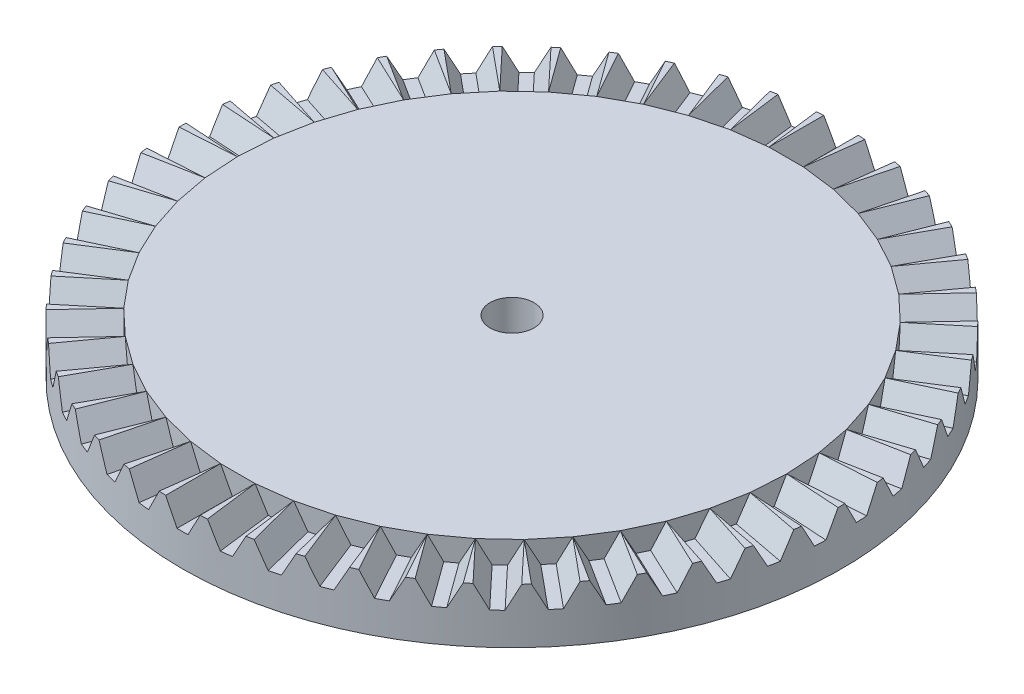
SolidWorks part; units mm, degrees
ref_plane "Front Plane" through (0, 0, 0) normal (0, 0, 1) x (1, 0, 0)
ref_plane "Top Plane" through (0, 0, 0) normal (0, 1, 0) x (1, 0, 0)
ref_plane "Right Plane" through (0, 0, 0) normal (1, 0, 0) x (0, 0, -1)
sketch "Foot Measurements" [suppressed] plane through (0, 0, 0) normal (0, 1, 0) x (1, 0, 0)
  line L0 (0, 0) -> (0, 73) construction
  line L1 (0, 0) -> (0, 147) construction
  line L2 (0, 0) -> (33, 0) construction
  line L3 (0, 0) -> (75, 0) construction
  line L4 (0, 73) -> (33, 73) construction
  line L5 (33, 73) -> (33, 0) construction
  line L6 (0, 147) -> (75, 147) construction
  line L7 (75, 147) -> (75, 0) construction
  line L8 (0, -100) -> (250, -100) construction
  line L9 (0, -100) -> (173, -100) construction
  dimension "D1" = 33
  dimension "D2" = 75
  dimension "D3" = 73
  dimension "D4" = 147
sketch "Sketch3" plane through (0, 0, 0) normal (0, 1, 0) x (1, 0, 0)
  circle A0 centre (0, 0) radius 30
extrude "Boss-Extrude3" add sketch "Sketch3" along normal blind 5
sketch "Sketch6" plane through (0, 5, 0) normal (0, 1, 0) x (1, 0, 0)
  circle A1 centre (0, 0) radius 2
  dimension "D1" = 4
extrude "Cut-Extrude1" cut sketch "Sketch6" against normal up to next
sketch "Sketch5" plane through (0, 5, 0) normal (0, 1, 0) x (1, 0, 0)
  line L0 (-1.5701, 29.9589) -> (-1.5701, 24.9589)
  line L1 (-1.5701, 24.9589) -> (1.5701, 24.9589)
  line L2 (1.5701, 24.9589) -> (1.5701, 29.9589)
  line L4 (0, 0) -> (-1.5701, 29.9589) construction
  line L5 (0, 0) -> (1.5701, 29.9589) construction
  circle A1 centre (0, 0) radius 30 construction
  arc A2 (1.5701, 29.9589) -> (-1.5701, 29.9589) centre (0, 0) ccw
  dimension "D1" = 3.1402
  dimension "D2" = 6
  dimension "D3" = 5
extrude "Cut-Extrude2" cut sketch "Sketch5" against normal blind 3
sketch "Sketch7" plane through (0, 0, -24.9589) normal (0, 0, -1) x (-1, 0, 0)
  line L0 (-1.5701, 2) -> (1.5701, 2)
  line L1 (1.5701, 2) -> (1.5701, 5)
  line L2 (1.5701, 5) -> (0.4972, 2.95)
  line L3 (-0.4972, 2.95) -> (-1.5701, 5)
  line L4 (-1.5701, 2) -> (-1.5701, 5)
  line L5 (-0.4972, 2.95) -> (0.4972, 2.95)
  dimension "D1" = 0.95
extrude "Boss-Extrude4" add sketch "Sketch7" along normal up to surface (5 mm away)
pattern_circular "CirPattern1" count 50 over 360 about axis through (0, 0, 0) along (0, 1, 0) of "Boss-Extrude4", "Cut-Extrude2"
